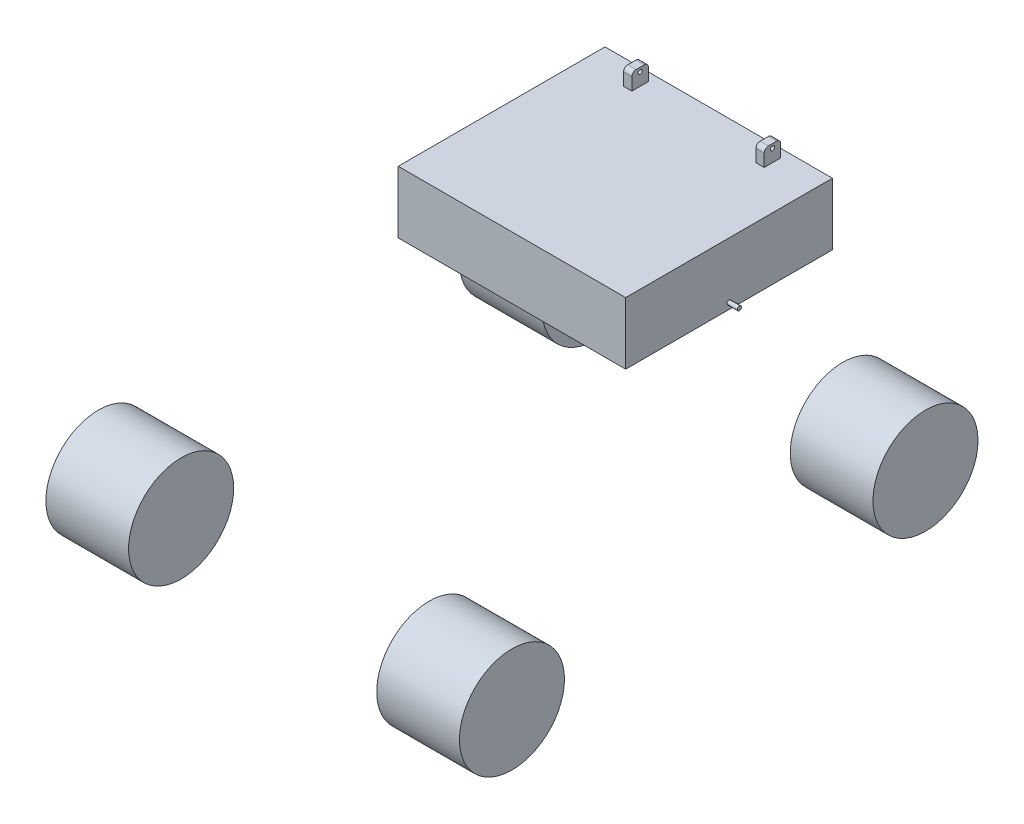
SolidWorks part; units mm, degrees
ref_plane "Front Plane" through (0, 0, 0) normal (0, 0, 1) x (1, 0, 0)
ref_plane "Top Plane" through (0, 0, 0) normal (0, 1, 0) x (1, 0, 0)
ref_plane "Right Plane" through (0, 0, 0) normal (1, 0, 0) x (0, 0, -1)
ref_plane "Plane1" through (300, 0, 0) normal (1, 0, 0) x (0, 0, -1)
sketch "Sketch2" plane through (300, 0, 0) normal (1, 0, 0) x (0, 0, -1)
  line L0 (-500, 0) -> (500, 0) construction
  circle A0 centre (-500, 0) radius 127
  circle A1 centre (500, 0) radius 127
  dimension "D1" = 254
  dimension "D2" = 1000
extrude "Boss-Extrude1" add sketch "Sketch2" along normal blind 200
mirror "Mirror4" about plane through (0, 0, 0) normal (1, 0, 0) of bodies 101 102
sketch "Sketch3" plane through (0, 0, 0) normal (1, 0, 0) x (0, 0, -1)
  line L1 (0, 500) -> (500, 500)
  line L2 (0, 500) -> (0, 350)
  line L3 (0, 350) -> (500, 350)
  line L4 (500, 500) -> (500, 350)
  point P4 (10.7223, 224.4541)
  point P5 (0, 333.107)
  dimension "D1" = 500
  dimension "D2" = 150
  dimension "D3" = 350
extrude "Boss-Extrude2" add sketch "Sketch3" along normal mid plane 550 separate body
sketch "Sketch4" plane through (275, 0, 0) normal (1, 0, 0) x (0, 0, -1)
  line L0 (0, 350) -> (500, 350) construction
  line L1 (250, 500) -> (250, 365) construction
  line L2 (500, 500) -> (0, 500) construction
  circle A0 centre (250, 365) radius 5
  dimension "D1" = 15
  dimension "D2" = 10
extrude "Boss-Extrude3" add sketch "Sketch4" along normal up to surface (25 mm away) up to face at (300, 0, -627)
mirror "Mirror6" about plane through (0, 0, 0) normal (1, 0, 0) of "Boss-Extrude3"
sketch "Sketch5" plane through (0, 500, 0) normal (0, 1, 0) x (1, 0, 0)
  line L0 (-215, 490) -> (215, 490)
  line L1 (-210, 485) -> (210, 485)
  line L2 (-210, 485) -> (-210, 245)
  line L3 (-210, 245) -> (210, 245)
  line L4 (210, 485) -> (210, 245)
  line L5 (215, 490) -> (215, 240)
  line L6 (-215, 240) -> (215, 240)
  line L7 (-215, 490) -> (-215, 240)
  line L8 (0, 0) -> (0, 240) construction
  dimension "D1" = 5
  dimension "D2" = 240
  dimension "D3" = 430
  dimension "D4" = 250
sketch "Sketch6" plane through (0, 500, 0) normal (0, 1, 0) x (1, 0, 0)
  line L0 (-150, 460) -> (150, 460) construction
  line L1 (-170, 440) -> (-150, 440)
  line L2 (-170, 440) -> (-170, 480)
  line L3 (-170, 480) -> (-150, 480)
  line L4 (-150, 440) -> (-150, 480)
  line L5 (150, 440) -> (170, 440)
  line L6 (150, 440) -> (150, 480)
  line L7 (150, 480) -> (170, 480)
  line L8 (170, 440) -> (170, 480)
  line L9 (0, 0) -> (0, 460) construction
  dimension "D1" = 300
  dimension "D2" = 40
  dimension "D3" = 20
  dimension "D4" = 460
extrude "Boss-Extrude4" add sketch "Sketch6" along normal blind 40
fillet "Fillet1" radius 10 4 edges at (160, 540, -440) (160, 540, -480) (-160, 540, -440) (-160, 540, -480)
sketch "Sketch7" plane through (170, 0, 0) normal (1, 0, 0) x (0, 0, -1)
  line L0 (460, 540) -> (460, 530) construction
  line L1 (450, 540) -> (470, 540) construction
  circle A0 centre (460, 530) radius 5
  dimension "D1" = 10
  dimension "D2" = 10
extrude "Cut-Extrude1" cut sketch "Sketch7" against normal through all
sketch "Sketch8" plane through (0, 0, 0) normal (1, 0, 0) x (0, 0, -1)
  line L0 (-130, 350) -> (-891.8102, -49.5089)
  line L1 (170, 550) -> (170, 1010) construction
  line L2 (379.7754, 881.1254) -> (375.0079, 531.1578) construction
  line L3 (170, 1010) -> (-891.8102, -49.5089)
  line L4 (170, 1010) -> (-891.8102, -49.5089) construction
  line L5 (219.4437, 960.4489) -> (-842.3665, -99.06) construction
  line L6 (120.5563, 1059.5511) -> (-941.254, 0.0423) construction
  line L7 (0, 0) -> (500, 0) construction
  line L8 (460, 530) -> (290.0158, 532.3157)
  line L9 (-519.0609, -125.5615) -> (-1143.494, -125.5615) construction
  line L10 (500, 500) -> (0, 500) construction
  line L11 (0, 500) -> (0, 350) construction
  line L12 (179.794, 883.8497) -> (290.0158, 532.3157)
  line L14 (460, 530) -> (579.7569, 878.401)
  line L15 (579.7569, 878.401) -> (179.794, 883.8497)
  circle A0 centre (-130, 350) radius 860.2105 construction
  circle A1 centre (170, 550) radius 460 construction
  arc A2 (219.4437, 960.4489) -> (120.5563, 1059.5511) centre (170, 1010) ccw construction
  arc A3 (-941.254, 0.0423) -> (-842.3665, -99.06) centre (-891.8102, -49.5089) ccw construction
  circle A4 centre (-500, 0) radius 127 construction
  point P6 (-360.9051, 480.2456)
  point P11 (0, 350)
  point P27 (299.3282, 530)
  point P31 (181.1789, 834.4253)
  point P32 (297.9357, 581.3338)
  point P33 (201.0315, 867.695)
  point P34 (733.3461, 761.837)
  point P35 (181.1789, 900.9138)
  point P36 (0, 0)
  point P37 (375.0079, 531.1578)
  point P38 (181.1789, 881.1254)
  point P39 (163.1544, 1002.4216)
  point P40 (131.1161, 1007.1511)
  point P41 (519.8784, 666.4117)
  point P42 (179.794, 999.0437)
  point P43 (-933.7912, -47.6773)
  point P46 (128.7345, 1009.1017)
  point P47 (-904.1211, -47.0346)
  point P48 (100, 1010)
  point P49 (140.3363, 1008.2281)
  point P50 (-1119.6899, 244.0366)
  point P51 (-886.356, -54.9469)
  point P52 (-889.4843, -51.8347)
  point P53 (-891.8102, -49.5089)
  dimension "D1" = 70
  dimension "D4" = 1500
  dimension "D2" = 170
  dimension "D3" = 130
  dimension "D6" = 50
  dimension "D7" = 170
  dimension "D8" = 460
  dimension "D9" = 400
  dimension "D10" = 350
